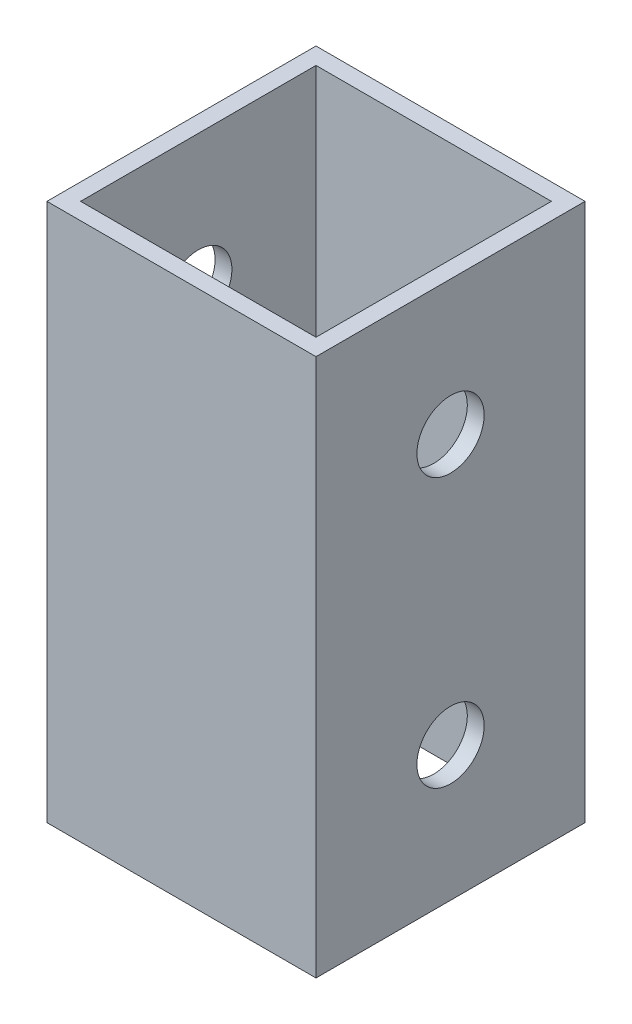
SolidWorks part; units mm, degrees
ref_plane "Front Plane" through (0, 0, 0) normal (0, 0, 1) x (1, 0, 0)
ref_plane "Top Plane" through (0, 0, 0) normal (0, 1, 0) x (1, 0, 0)
ref_plane "Right Plane" through (0, 0, 0) normal (1, 0, 0) x (0, 0, -1)
sketch "Sketch1" plane through (0, 0, 0) normal (0, 1, 0) x (1, 0, 0)
  line L1 (-12.7, -12.7) -> (12.7, -12.7)
  line L2 (-12.7, -12.7) -> (-12.7, 12.7)
  line L3 (-12.7, 12.7) -> (12.7, 12.7)
  line L4 (12.7, -12.7) -> (12.7, 12.7)
  line L5 (-12.7, -12.7) -> (12.7, 12.7) construction
  line L6 (-12.7, 12.7) -> (12.7, -12.7) construction
  line L7 (11.1125, -11.1125) -> (-11.1125, -11.1125)
  line L8 (11.1125, -11.1125) -> (11.1125, 11.1125)
  line L9 (11.1125, 11.1125) -> (-11.1125, 11.1125)
  line L10 (-11.1125, -11.1125) -> (-11.1125, 11.1125)
  line L11 (11.1125, -11.1125) -> (-11.1125, 11.1125) construction
  line L12 (11.1125, 11.1125) -> (-11.1125, -11.1125) construction
  point P0 (0, 0)
  point P6 (0, 0)
  dimension "D1" = 25.4
  dimension "D2" = 25.4
  dimension "D3" = 1.5875
extrude "Boss-Extrude1" add sketch "Sketch1" along normal blind 50.8
sketch "Sketch2" plane through (12.7, 0, 0) normal (1, 0, 0) x (0, 0, -1)
  line L0 (0, 0) -> (0, 12.7) construction
  line L1 (0, 12.7) -> (0, 38.1) construction
  line L2 (0, 38.1) -> (0, 50.8) construction
  line L3 (-12.7, 50.8) -> (12.7, 50.8) construction
  circle A0 centre (0, 38.1) radius 3.175
  circle A1 centre (0, 12.7) radius 3.175
  dimension "D2" = 6.35
  dimension "D1" = 25.4
extrude "Cut-Extrude1" cut sketch "Sketch2" against normal through all
